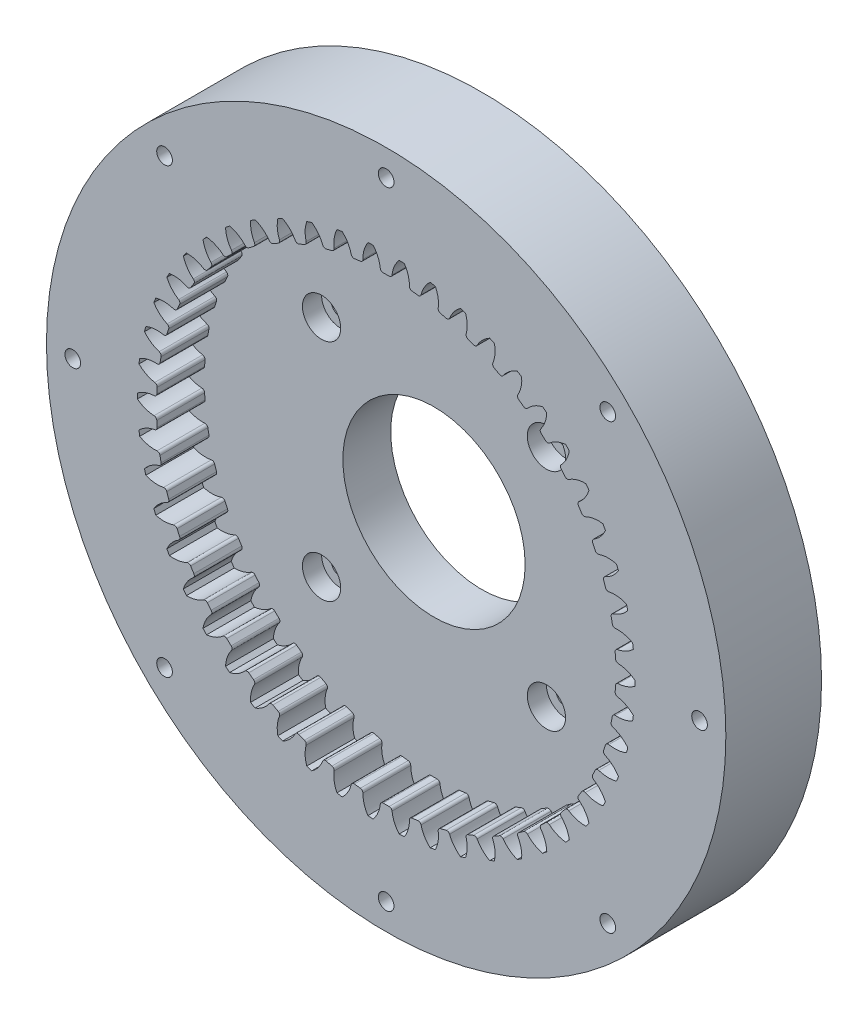
SolidWorks part; units mm, degrees
ref_plane "Front Plane" through (0, 0, 0) normal (0, 0, 1) x (1, 0, 0)
ref_plane "Top Plane" through (0, 0, 0) normal (0, 1, 0) x (1, 0, 0)
ref_plane "Right Plane" through (0, 0, 0) normal (1, 0, 0) x (0, 0, -1)
sketch "Sketch1" plane through (0, 0, 0) normal (0, 0, 1) x (1, 0, 0)
  circle A0 centre (0, 0) radius 60
  dimension "D1" = 120
extrude "Boss-Extrude1" add sketch "Sketch1" along normal blind 10
sketch "Sketch5" plane through (0, 0, 0) normal (0, 0, -1) x (-1, 0, 0)
  arc A1 (2.7166, 51.929) -> (1.2312, 48.5289) centre (7.4674, 47.829) ccw
  arc A2 (3.8132, 51.86) -> (2.7166, 51.929) centre (0, 0) ccw
  arc A3 (5.3933, 47.696) -> (0.6271, 47.9959) centre (0, 0) ccw
  circle A5 centre (0, 0) radius 48 construction
  arc A8 (4.8608, 48.3006) -> (5.3933, 47.696) centre (5.4607, 48.2922) ccw
  arc A9 (0.6271, 47.9959) -> (1.2312, 48.5289) centre (0.635, 48.5959) ccw
  arc A12 (4.8608, 48.3006) -> (3.8132, 51.86) centre (-1.414, 48.3878) ccw
  dimension "D1" = 96
extrude "Cut-Extrude2" cut sketch "Sketch5" against normal through all
pattern_circular "CirPattern2" count 50 over 360 about axis through (0, 0, 0) along (0, 0, 1) of "Cut-Extrude2"
sketch "Sketch6" plane through (0, 0, 0) normal (0, 0, -1) x (-1, 0, 0)
  circle A0 centre (0, 0) radius 48
  dimension "D1" = 96
extrude "Cut-Extrude3" cut sketch "Sketch6" against normal through all
sketch "Sketch7" plane through (0, 0, 0) normal (0, 0, -1) x (-1, 0, 0)
  circle A0 centre (0, 0) radius 60
extrude "Boss-Extrude2" add sketch "Sketch7" along normal blind 10
sketch "Sketch8" plane through (0, 0, 0) normal (0, 0, 1) x (1, 0, 0)
  line L1 (23.5, -23.5) -> (-23.5, -23.5) construction
  line L2 (23.5, -23.5) -> (23.5, 23.5) construction
  line L3 (23.5, 23.5) -> (-23.5, 23.5) construction
  line L4 (-23.5, -23.5) -> (-23.5, 23.5) construction
  line L5 (23.5, -23.5) -> (-23.5, 23.5) construction
  line L6 (23.5, 23.5) -> (-23.5, -23.5) construction
  circle A0 centre (0, 0) radius 19.05
  circle A1 centre (-23.5, 23.5) radius 2
  circle A2 centre (23.5, 23.5) radius 2
  circle A3 centre (23.5, -23.5) radius 2
  circle A4 centre (-23.5, -23.5) radius 2
  dimension "D1" = 38.1
  dimension "D3" = 4
  dimension "D2" = 47
extrude "Cut-Extrude4" cut sketch "Sketch8" against normal through all
sketch "Sketch9" plane through (0, 0, 0) normal (0, 0, 1) x (1, 0, 0)
  circle A0 centre (-23.5, 23.5) radius 4
  circle A1 centre (23.5, 23.5) radius 4
  circle A2 centre (23.5, -23.5) radius 4
  circle A3 centre (-23.5, -23.5) radius 4
  dimension "D1" = 8
extrude "Cut-Extrude5" cut sketch "Sketch9" against normal blind 4
sketch "Sketch10" plane through (0, 0, -10) normal (0, 0, -1) x (-1, 0, 0)
  line L0 (-71, 0) -> (-65.5, 0) construction
  line L1 (-65.5, 0) -> (-60, 0) construction
  circle A0 centre (0, 0) radius 71
  circle A1 centre (0, 0) radius 65.5 construction
  circle A2 centre (0, 0) radius 60 construction
  circle A3 centre (0, 65.5) radius 1.637
  circle A4 centre (46.3155, 46.3155) radius 1.637
  circle A5 centre (65.5, 0) radius 1.637
  circle A6 centre (46.3155, -46.3155) radius 1.637
  circle A7 centre (0, -65.5) radius 1.637
  circle A8 centre (-46.3155, -46.3155) radius 1.637
  circle A9 centre (-65.5, 0) radius 1.637
  circle A10 centre (-46.3155, 46.3155) radius 1.637
  circle A11 centre (0, 0) radius 60
  point P29 (0, 0)
  dimension "D1" = 142
  dimension "D2" = 3.2741
  dimension "D3" = 8
extrude "Boss-Extrude3" add sketch "Sketch10" against normal through all
sketch "Sketch11" plane through (0, 0, -10) normal (0, 0, -1) x (-1, 0, 0)
  line L1 (-3.6438, 65.7142) -> (-2.0074, 62.4515)
  line L2 (-2.0074, 62.4515) -> (1.6363, 62.2373)
  line L3 (1.6363, 62.2373) -> (3.6438, 65.2858)
  line L4 (3.6438, 65.2858) -> (2.0074, 68.5485)
  line L5 (2.0074, 68.5485) -> (-1.6363, 68.7627)
  line L6 (-1.6363, 68.7627) -> (-3.6438, 65.7142)
  circle A0 centre (0, 65.5) radius 3.161 construction
  point P1 (2.8256, 66.9171)
  dimension "D1" = 6.3221
extrude "Cut-Extrude6" cut sketch "Sketch11" against normal blind 10.3114
pattern_circular "CirPattern3" count 8 over 360 about axis through (0, 0, 0) along (0, 0, 1) of "Cut-Extrude6"
